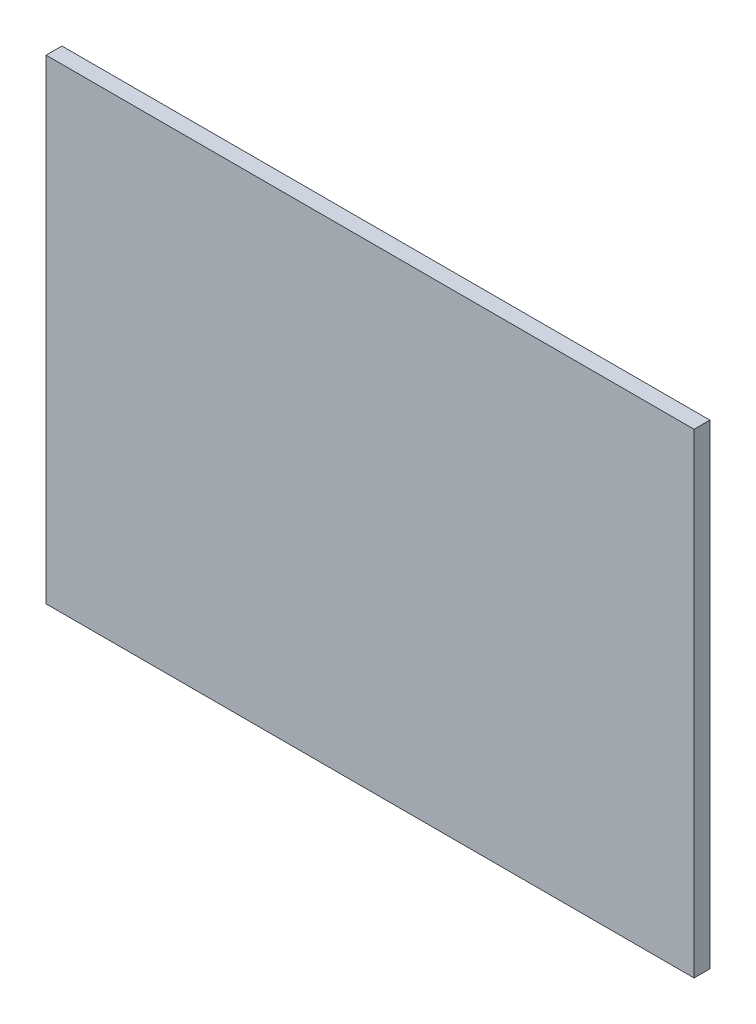
SolidWorks part; units mm, degrees
ref_plane "Face" through (0, 0, 0) normal (0, 0, 1) x (1, 0, 0)
ref_plane "Dessus" through (0, 0, 0) normal (0, 1, 0) x (1, 0, 0)
ref_plane "Droite" through (0, 0, 0) normal (1, 0, 0) x (0, 0, -1)
sketch "Esquisse1" plane through (0, 0, 0) normal (0, 0, 1) x (1, 0, 0)
  line L1 (0, 0) -> (204.5301, 0)
  line L2 (0, 0) -> (0, 150)
  line L3 (0, 150) -> (204.5301, 150)
  line L4 (204.5301, 0) -> (204.5301, 150)
  dimension "D1" = 150
  dimension "D2" = 204.5301
extrude "Boss.-Extru.1" add sketch "Esquisse1" along normal blind 5
sketch "Esquisse2" plane through (0, 0, 0) normal (0, 0, -1) x (-1, 0, 0)
  line L0 (-102.2651, 0) -> (-102.2651, 261.3781)
  line L1 (0, 0) -> (-204.5301, 0) construction
  line L2 (0, 75) -> (-204.5301, 75)
  line L3 (0, 150) -> (0, 0) construction
  line L4 (-204.5301, 0) -> (-204.5301, 150) construction
